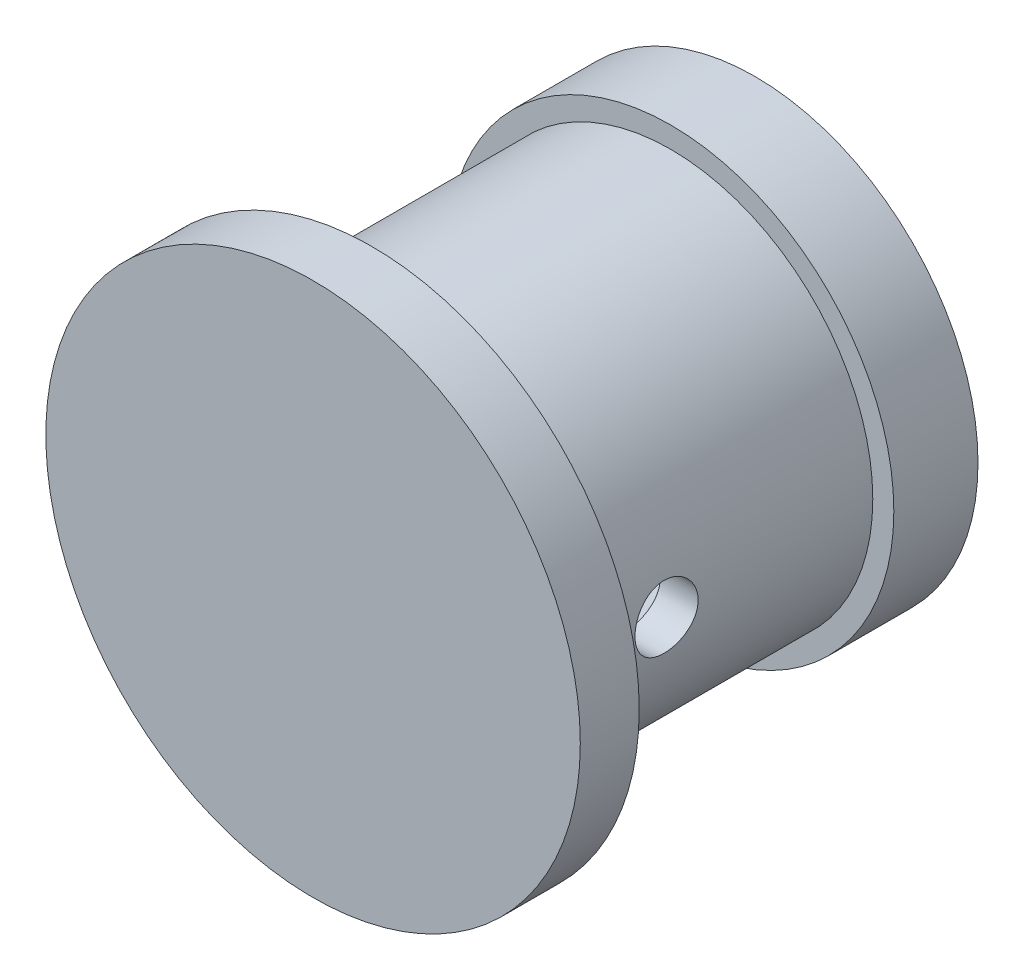
SolidWorks part; units mm, degrees
ref_plane "Front Plane" through (0, 0, 0) normal (0, 0, 1) x (1, 0, 0)
ref_plane "Top Plane" through (0, 0, 0) normal (0, 1, 0) x (1, 0, 0)
ref_plane "Right Plane" through (0, 0, 0) normal (1, 0, 0) x (0, 0, -1)
sketch "Sketch1" plane through (0, 0, 0) normal (0, 0, 1) x (1, 0, 0)
  circle A0 centre (0, 0) radius 3.9
  circle A1 centre (0, 0) radius 5.3
extrude "Extrude1" add sketch "Sketch1" along normal blind 2
sketch "Sketch2" plane through (0, 0, 2) normal (0, 0, 1) x (1, 0, 0)
  circle A0 centre (0, 0) radius 3.9
  circle A1 centre (0, 0) radius 4.8
extrude "Extrude2" add sketch "Sketch2" along normal blind 7.5
sketch "Sketch4" plane through (0, 0, 0) normal (1, 0, 0) x (0, 0, -1)
  line L0 (-9.5, 4.8) -> (-9.5, -4.8) construction
  circle A0 centre (-6.9, 0) radius 0.75
  dimension "D1" = 2.6
extrude "Extrude3" cut sketch "Sketch4" against normal through all and the other way through all
sketch "Sketch5" plane through (0, 0, 9.5) normal (0, 0, 1) x (1, 0, 0)
  circle A0 centre (0, 0) radius 6.35
extrude "Extrude4" add sketch "Sketch5" along normal blind 1 and the other way blind 0.4
